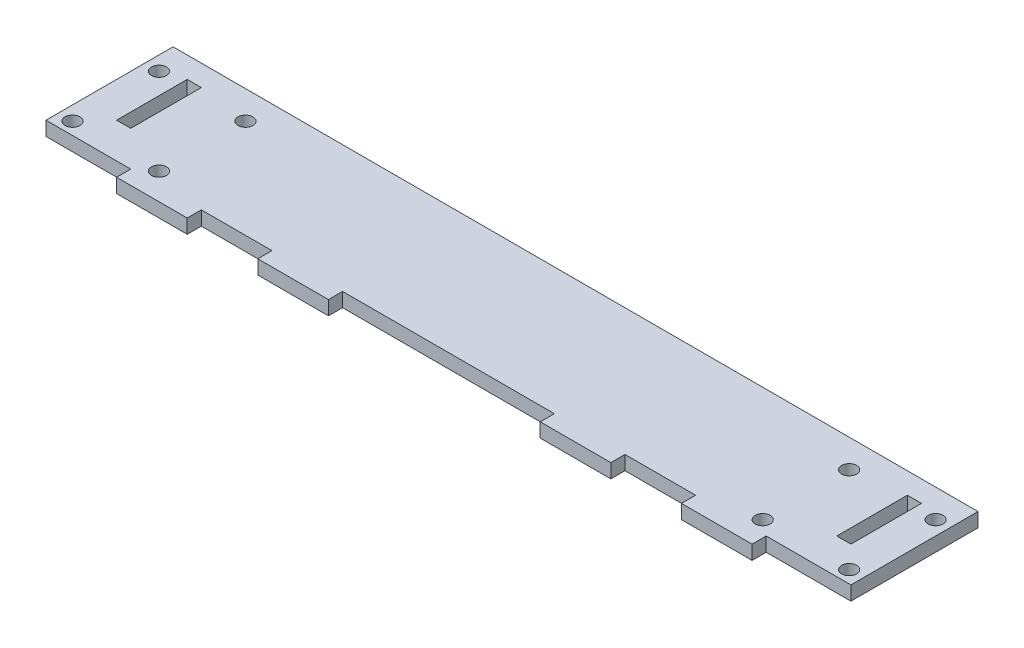
SolidWorks part; units mm, degrees
ref_plane "Front" through (0, 0, 0) normal (0, 0, 1) x (1, 0, 0)
ref_plane "Top" through (0, 0, 0) normal (0, 1, 0) x (1, 0, 0)
ref_plane "Right" through (0, 0, 0) normal (1, 0, 0) x (0, 0, -1)
sketch "Sketch1" plane through (0, 0, 0) normal (0, 1, 0) x (1, 0, 0)
  line L0 (64, 0) -> (84, 0)
  line L5 (0, 0) -> (228, 0)
  line L6 (0, 0) -> (0, 36)
  line L11 (0, 36) -> (228, 36)
  line L12 (228, 0) -> (228, 36)
  line L13 (24, 0) -> (44, 0)
  line L14 (24, 0) -> (24, -4)
  line L15 (24, -4) -> (44, -4)
  line L16 (44, 0) -> (44, -4)
  line L25 (64, 0) -> (64, -4)
  line L26 (64, -4) -> (84, -4)
  line L27 (84, 0) -> (84, -4)
  line L28 (104, 0) -> (124, 0)
  line L29 (104, 0) -> (104, -4)
  line L30 (104, -4) -> (124, -4)
  line L31 (124, 0) -> (124, -4)
  line L32 (144, 0) -> (164, 0)
  line L33 (144, 0) -> (144, -4)
  line L34 (144, -4) -> (164, -4)
  line L35 (164, 0) -> (164, -4)
  line L36 (184, 0) -> (204, 0)
  line L37 (184, 0) -> (184, -4)
  line L38 (184, -4) -> (204, -4)
  line L39 (204, 0) -> (204, -4)
  line L40 (114, 61.9803) -> (114, -21.7588) construction
  line L41 (10, 30) -> (14, 30)
  line L42 (10, 30) -> (10, 10)
  line L43 (10, 10) -> (14, 10)
  line L44 (14, 30) -> (14, 10)
  line L45 (214, 30) -> (214, 10)
  line L46 (218, 10) -> (214, 10)
  line L47 (218, 30) -> (218, 10)
  line L48 (218, 30) -> (214, 30)
  line L49 (4, 28) -> (4, 3.5) construction
  line L50 (224, 28) -> (224, 3.5) construction
  line L51 (28.5, 28) -> (28.5, 3.5) construction
  line L52 (4, 28) -> (28.5, 28) construction
  line L53 (224, 28) -> (199.5, 28) construction
  line L54 (199.5, 28) -> (199.5, 3.5) construction
  circle A0 centre (4, 3.5) radius 2.125
  circle A1 centre (4, 28) radius 2.125
  circle A2 centre (224, 28) radius 2.125
  circle A3 centre (224, 3.5) radius 2.125
  circle A4 centre (28.5, 3.5) radius 2.125
  circle A5 centre (28.5, 28) radius 2.125
  circle A6 centre (199.5, 28) radius 2.125
  circle A7 centre (199.5, 3.5) radius 2.125
  point P17 (24, -2)
  dimension "D11" = 4.25
  dimension "D12" = 24.5
  dimension "D1" = 36
  dimension "D2" = 228
  dimension "D3" = 20
  dimension "D4" = 4
  dimension "D5" = 24
  dimension "D7" = 6
  dimension "D8" = 10
  dimension "D9" = 4
  dimension "D10" = 20
  dimension "D13" = 3.5
  dimension "D14" = 4
  dimension "D15" = 24.5
  dimension "D6" = 5
extrude "Boss-Extrude2" add sketch "Sketch1" along normal blind 4 contours L5 L12 L11 L6 L0 | L35 L5 L33 L34 | L39 L5 L37 L38 | L40 L11 L6 L5 L0 L41 L44 L43 L42 | L16 L5 L14 L15
